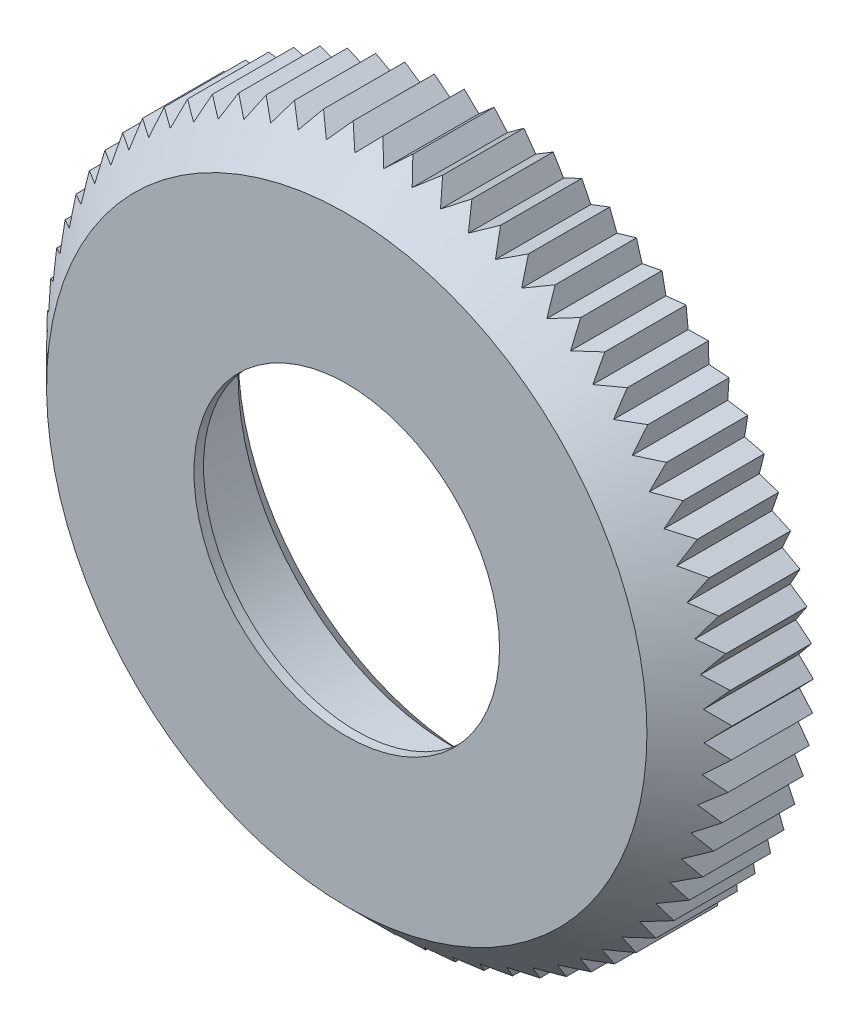
SolidWorks part; units mm, degrees
ref_plane "Plan de face" through (0, 0, 0) normal (0, 0, 1) x (1, 0, 0)
ref_plane "Plan de dessus" through (0, 0, 0) normal (0, 1, 0) x (1, 0, 0)
ref_plane "Plan de droite" through (0, 0, 0) normal (1, 0, 0) x (0, 0, -1)
sketch "Esquisse1" plane through (0, 0, 0) normal (0, 0, 1) x (1, 0, 0)
  circle A0 centre (0, 0) radius 8.0164
  circle A1 centre (0, 0) radius 17.25
  dimension "D1" = 34.5
extrude "Boss.-Extru.1" add sketch "Esquisse1" along normal blind 0.5
sketch "Esquisse2" plane through (0, 0, 0) normal (0, 0, -1) x (-1, 0, 0)
  circle A0 centre (0, 0) radius 17.25
  circle A1 centre (0, 0) radius 11.2
  circle A2 centre (0, 0) radius 11 construction
  circle A3 centre (0, 0) radius 17.25 construction
  dimension "D1" = 0.2
extrude "Boss.-Extru.2" add sketch "Esquisse2" along normal blind 6
chamfer "Chanfrein1" distance 1 angle 45 1 edges at (-11.2, 0, -6)
chamfer "Chanfrein2" distance 1.5 angle 45 1 edges at (17.25, 0, 0.5)
sketch "Esquisse3" plane through (0, 0, -6) normal (0, 0, -1) x (-1, 0, 0)
  line L0 (0, 0) -> (-1.9326, 17.1414)
  line L1 (-1.9326, 17.1414) -> (-1.2335, 17.9437)
  line L2 (-1.2335, 17.9437) -> (-0.4312, 17.2446)
  line L3 (-0.4312, 17.2446) -> (0, 0)
  circle A0 centre (0, 0) radius 17.25 construction
  arc A1 (-1.3668, 12.1232) -> (-0.305, 12.1962) centre (0, 0) cw
  circle A2 centre (0, 0) radius 12.2 construction
  circle M6 centre (0, 0) radius 17.25
  dimension "D1" = 5
extrude "Boss.-Extru.3" add sketch "Esquisse3" against normal up to surface (5 mm away) contours L2 L1 M6 up to face at (17.25, 0, -1)
pattern_circular "Répétition circulaire1" count 72 every 5 about axis through (0, 0, 0) along (0, 0, 1) of "Boss.-Extru.3"
sketch "Esquisse4" plane through (0, 0, -6) normal (0, 0, -1) x (-1, 0, 0)
  circle A0 centre (0, 0) radius 17.986
